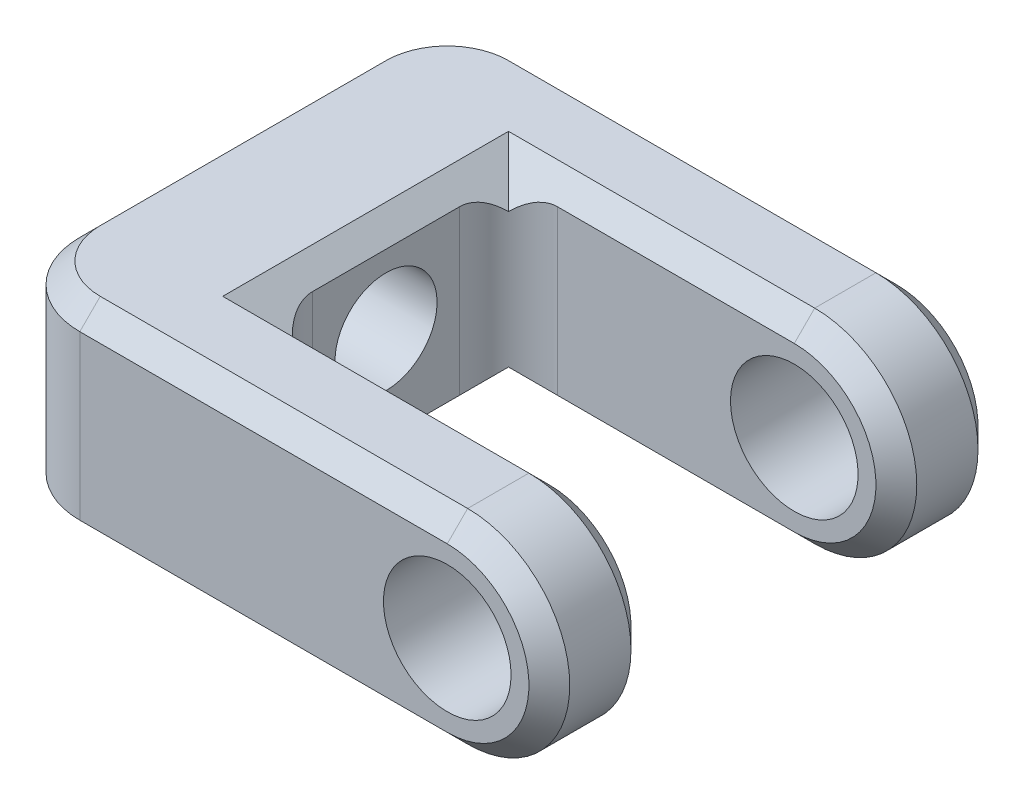
SolidWorks part; units mm, degrees
material "Plain Carbon Steel"
ref_plane "Front" through (0, 0, 0) normal (0, 0, 1) x (1, 0, 0)
ref_plane "Top" through (0, 0, 0) normal (0, 1, 0) x (1, 0, 0)
ref_plane "Right" through (0, 0, 0) normal (1, 0, 0) x (0, 0, -1)
sketch "Sketch1" plane through (0, 0, 0) normal (0, 0, 1) x (1, 0, 0)
  line L1 (0, 0) -> (34.925, 0)
  line L2 (0, 0) -> (0, 15.875)
  line L3 (0, 15.875) -> (34.925, 15.875)
  arc A0 (34.925, 0) -> (34.925, 15.875) centre (34.925, 7.9375) ccw
  circle A1 centre (34.925, 7.9375) radius 4.9609
  dimension "D1" = 9.9219
  dimension "D2" = 15.875
  dimension "D3" = 34.925
extrude "Boss-Extrude1" add sketch "Sketch1" along normal blind 34.925
sketch "Sketch2" plane through (0, 15.875, 0) normal (0, 1, 0) x (1, 0, 0)
  line L0 (42.8625, -34.925) -> (42.8625, 0) construction
  line L1 (12.7, -7.9375) -> (42.8625, -7.9375)
  line L2 (12.7, -7.9375) -> (12.7, -26.9875)
  line L3 (12.7, -26.9875) -> (42.8625, -26.9875)
  line L4 (42.8625, -7.9375) -> (42.8625, -26.9875)
  line L5 (0, -34.925) -> (0, 0) construction
  line L6 (34.925, 0) -> (0, 0) construction
  dimension "D1" = 19.05
  dimension "D2" = 12.7
  dimension "D3" = 7.9375
extrude "Cut-Extrude1" cut sketch "Sketch2" against normal through all
sketch "Sketch3" plane through (0, 0, 0) normal (-1, 0, 0) x (0, 0, 1)
  line L0 (34.925, 0) -> (0, 0) construction
  line L1 (34.925, 15.875) -> (34.925, 0) construction
  circle A0 centre (17.4625, 8.7312) radius 3.9688
  dimension "D1" = 7.9375
  dimension "D2" = 8.7312
  dimension "D3" = 17.4625
extrude "Cut-Extrude2" cut sketch "Sketch3" against normal through all
fillet "Fillet1" radius 6.35 2 edges at (0, 7.9375, 0) (0, 7.9375, 34.925)
chamfer "Chamfer1" distance 1.5875 angle 45 20 edges at (23.8125, 0, 26.9875) (12.7, 0, 17.4625) (23.8125, 0, 7.9375) (20.6375, 0, 34.925) (1.8599, 0, 33.0651) (20.6375, 0, 0) (1.8599, 0, 1.8599) (0, 0, 17.4625) (42.8625, 7.9375, 7.9375) (42.8625, 7.9375, 26.9875) (23.8125, 15.875, 7.9375) (12.7, 15.875, 17.4625) (23.8125, 15.875, 26.9875) (42.8625, 7.9375, 34.925) (42.8625, 7.9375, 0) (20.6375, 15.875, 34.925) (1.8599, 15.875, 33.0651) (0, 15.875, 17.4625) (1.8599, 15.875, 1.8599) (20.6375, 15.875, 0)
fillet "Fillet2" radius 3.81 2 edges at (12.7, 7.9375, 26.9875) (12.7, 7.9375, 7.9375)
equation "\"Total Cutting Length\"= \"Cutting Length-Outer\" + \"Cutting Length-Inner\""
equation "\"Amount in ft^2\"= \"Bounding Box Area-Blank\" / 144"
